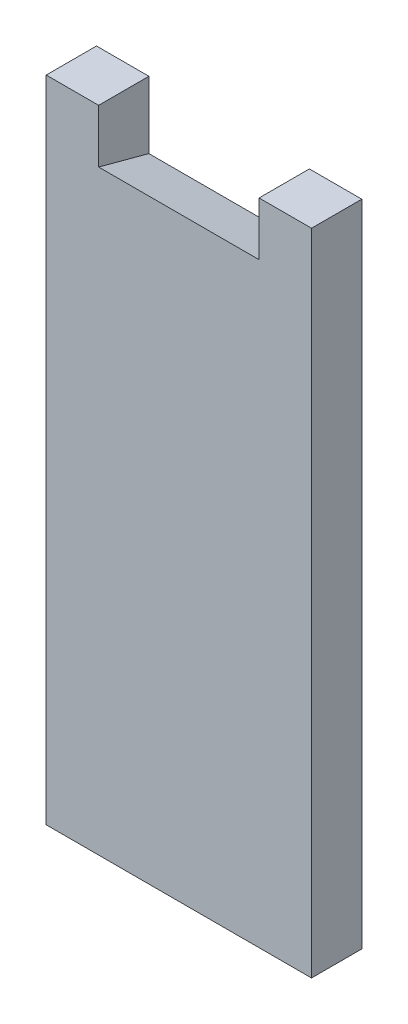
SolidWorks part; units mm, degrees
ref_plane "前视基准面" through (0, 0, 0) normal (0, 0, 1) x (1, 0, 0)
ref_plane "上视基准面" through (0, 0, 0) normal (0, 1, 0) x (1, 0, 0)
ref_plane "右视基准面" through (0, 0, 0) normal (1, 0, 0) x (0, 0, -1)
sketch "草图1" plane through (0, 0, 0) normal (0, 0, 1) x (1, 0, 0)
  line L1 (0, 0) -> (49.6, 0)
  line L2 (0, 0) -> (0, -121.4)
  line L3 (0, -121.4) -> (49.6, -121.4)
  line L4 (49.6, 0) -> (49.6, -121.4)
  line L5 (9.8, 0) -> (39.8, 0)
  line L6 (9.8, 0) -> (9.8, -10)
  line L7 (9.8, -10) -> (39.8, -10)
  line L8 (39.8, 0) -> (39.8, -10)
  point P9 (24.8, 0)
  dimension "D1" = 10
  dimension "D2" = 49.6
  dimension "D3" = 30
  dimension "D4" = 111.4
extrude "凸台-拉伸1" add sketch "草图1" along normal blind 9.4 contours L1 L8 L7 L6 L2 L3 L4
draft "拔模5" type of draft neutral plane draft angle 15 faces to draft 1 face at (24.8, -10, 4.7) neutral plane through (0, 0, 9.4) neutral plane normal (0, 0, 1) reverse direction yes parameters "D1"=15
